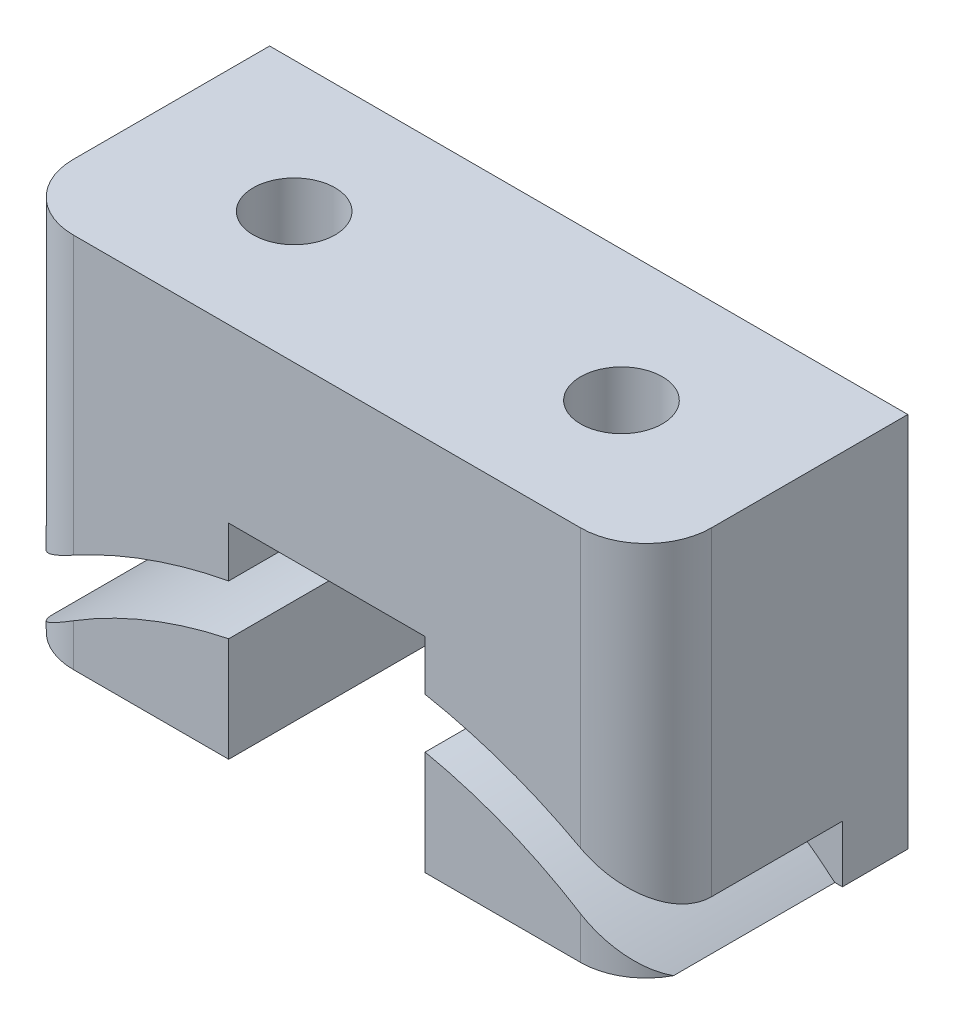
SolidWorks part; units mm, degrees
ref_plane "Front Plane" through (0, 0, 0) normal (0, 0, 1) x (1, 0, 0)
ref_plane "Top Plane" through (0, 0, 0) normal (0, 1, 0) x (1, 0, 0)
ref_plane "Right Plane" through (0, 0, 0) normal (1, 0, 0) x (0, 0, -1)
sketch "Sketch1" plane through (0, 0, 0) normal (0, 0, 1) x (1, 0, 0)
  line L1 (-9.75, -5) -> (9.75, -5)
  line L2 (-9.75, -5) -> (-9.75, 6.5)
  line L3 (-9.75, 6.5) -> (9.75, 6.5)
  line L4 (9.75, -5) -> (9.75, 6.5)
  point P0 (0, 0)
  dimension "D1" = 19.5
  dimension "D2" = 6.5
  dimension "D3" = 5
extrude "Boss-Extrude1" add sketch "Sketch1" along normal blind 8
fillet "Fillet1" radius 2 2 edges at (-9.75, 0.75, 8) (9.75, 0.75, 8)
sketch "Sketch2" plane through (0, 0, 8) normal (0, 0, 1) x (1, 0, 0)
  line L0 (0, 0) -> (0, -16.2) construction
  line L5 (0, -16.2) -> (0, -1.5) construction
  circle A0 centre (0, -16.2) radius 14.7
  circle A1 centre (0, -16.2) radius 16.2
  point P0 (0, 0)
  dimension "D4" = 16.2
  dimension "D5" = 14.7
extrude "Cut-Extrude1" cut sketch "Sketch2" against normal blind 6
sketch "Sketch3" plane through (0, 6.5, 0) normal (0, 1, 0) x (1, 0, 0)
  line L0 (-5, -4) -> (5, -4) construction
  line L1 (9.75, 0) -> (-9.75, 0) construction
  circle A0 centre (5, -4) radius 1.25
  circle A1 centre (-5, -4) radius 1.25
  point P4 (0, -4)
  point P9 (0, 0)
  dimension "D2" = 10
  dimension "D1" = 4
extrude "Cut-Extrude2" cut sketch "Sketch3" against normal up to next
sketch "Sketch4" plane through (0, 0, 0) normal (0, 0, -1) x (-1, 0, 0)
  line L0 (9.75, -5) -> (-9.75, -5) construction
  line L1 (-3, -11.25) -> (3, -11.25)
  line L2 (-3, -11.25) -> (-3, 1.25)
  line L3 (-3, 1.25) -> (3, 1.25)
  line L4 (3, -11.25) -> (3, 1.25)
  line L5 (-3, -11.25) -> (3, 1.25) construction
  line L6 (-3, 1.25) -> (3, -11.25) construction
  point P0 (0, -5)
  dimension "D1" = 6
  dimension "D2" = 12.5
extrude "Cut-Extrude3" cut sketch "Sketch4" against normal through all contours L1 L4 L3 L2
